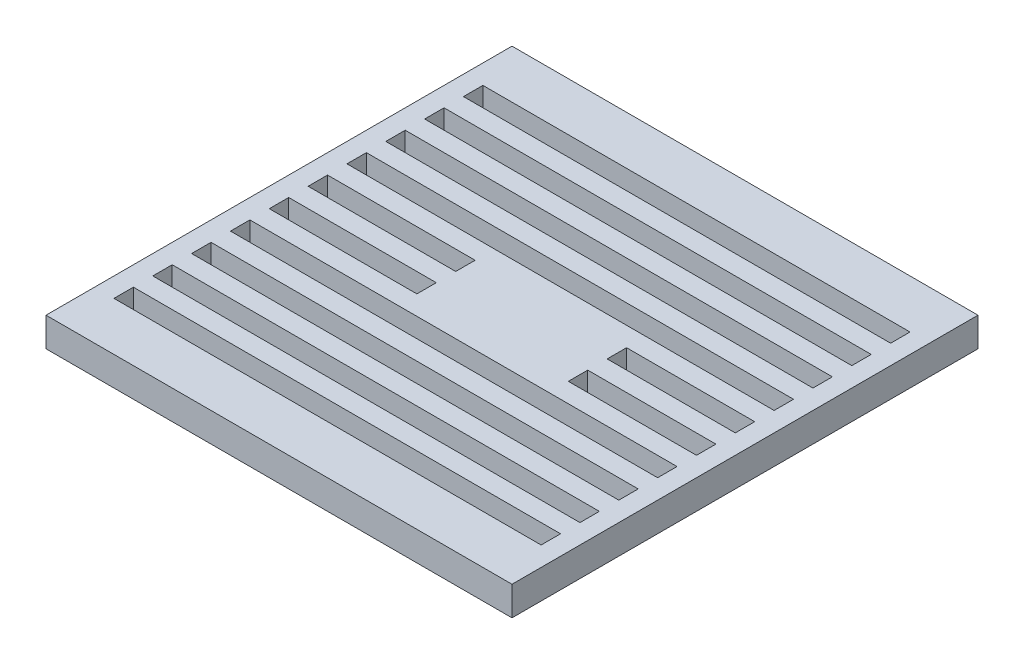
SolidWorks part; units mm, degrees
material "ABS"
ref_plane "Front Plane" through (0, 0, 0) normal (0, 0, 1) x (1, 0, 0)
ref_plane "Top Plane" through (0, 0, 0) normal (0, 1, 0) x (1, 0, 0)
ref_plane "Right Plane" through (0, 0, 0) normal (1, 0, 0) x (0, 0, -1)
sketch "Sketch1" plane through (0, 0, 0) normal (0, 1, 0) x (1, 0, 0)
  line L1 (-76.2, -76.2) -> (76.2, -76.2)
  line L2 (-76.2, -76.2) -> (-76.2, 76.2)
  line L3 (-76.2, 76.2) -> (76.2, 76.2)
  line L4 (76.2, -76.2) -> (76.2, 76.2)
  line L5 (0, 76.2) -> (0, -76.2) construction
  line L6 (-76.2, 0) -> (76.2, 0) construction
  point P0 (0, 0)
  dimension "D1" = 152.4
  dimension "D2" = 152.4
extrude "Boss-Extrude1" add sketch "Sketch1" along normal blind 9.525
sketch "Sketch2" plane through (0, 0, 0) normal (0, -1, 0) x (1, 0, 0)
  line L0 (-76.2, 76.2) -> (76.2, 76.2) construction
  line L1 (-69.85, 53.975) -> (69.85, 53.975)
  line L2 (-69.85, 53.975) -> (-69.85, 60.325)
  line L3 (-69.85, 60.325) -> (69.85, 60.325)
  line L4 (69.85, 53.975) -> (69.85, 60.325)
  line L5 (0, 60.325) -> (0, 53.975) construction
  line L6 (-69.85, 57.15) -> (69.85, 57.15) construction
  line L7 (76.2, 76.2) -> (76.2, -76.2) construction
  point P0 (0, 57.15)
  point P8 (0, 0)
  point P9 (0, 0)
  dimension "D1" = 15.875
  dimension "D2" = 6.35
  dimension "D3" = 6.35
extrude "Cut-Extrude1" cut sketch "Sketch2" against normal through all
pattern_linear "LPattern1" count 10 spacing 12.7 along (0, 0, -1) skipping (4, 0), (5, 0) of "Cut-Extrude1"
sketch "Sketch3" plane through (0, 0, 0) normal (0, -1, 0) x (1, 0, 0)
  line L0 (-69.85, 15.875) -> (69.85, 15.875) construction
  line L1 (-19.05, -15.875) -> (25.4, -15.875) construction
  line L2 (-19.05, -15.875) -> (-19.05, 15.875) construction
  line L3 (-19.05, 15.875) -> (25.4, 15.875) construction
  line L4 (25.4, -15.875) -> (25.4, 15.875) construction
  line L5 (3.175, 15.875) -> (3.175, -15.875) construction
  line L6 (-19.05, 0) -> (25.4, 0) construction
  line L7 (69.85, 53.975) -> (69.85, 60.325) construction
  line L8 (-69.85, 9.525) -> (-21.59, 9.525)
  line L9 (-69.85, 9.525) -> (-69.85, 3.175)
  line L10 (-69.85, 3.175) -> (-21.59, 3.175)
  line L11 (-21.59, 9.525) -> (-21.59, 3.175)
  line L12 (-45.72, 3.175) -> (-45.72, 9.525) construction
  line L13 (-69.85, 6.35) -> (-21.59, 6.35) construction
  line L14 (-69.85, 60.325) -> (-69.85, 53.975) construction
  line L15 (69.85, 3.175) -> (27.94, 3.175)
  line L16 (69.85, 3.175) -> (69.85, 9.525)
  line L17 (69.85, 9.525) -> (27.94, 9.525)
  line L18 (27.94, 3.175) -> (27.94, 9.525)
  line L19 (48.895, 9.525) -> (48.895, 3.175) construction
  line L20 (69.85, 6.35) -> (27.94, 6.35) construction
  point P0 (0, 0)
  point P11 (48.895, 6.35)
  point P348 (-45.72, 6.35)
  dimension "D1" = 44.45
  dimension "D2" = 6.35
  dimension "D3" = 2.54
  dimension "D4" = 19.05
  dimension "D5" = 2.54
extrude "Cut-Extrude2" cut sketch "Sketch3" against normal blind 9.525
pattern_linear "LPattern2" count 2 spacing 12.7 along (0, 0, -1) of "Cut-Extrude2"
